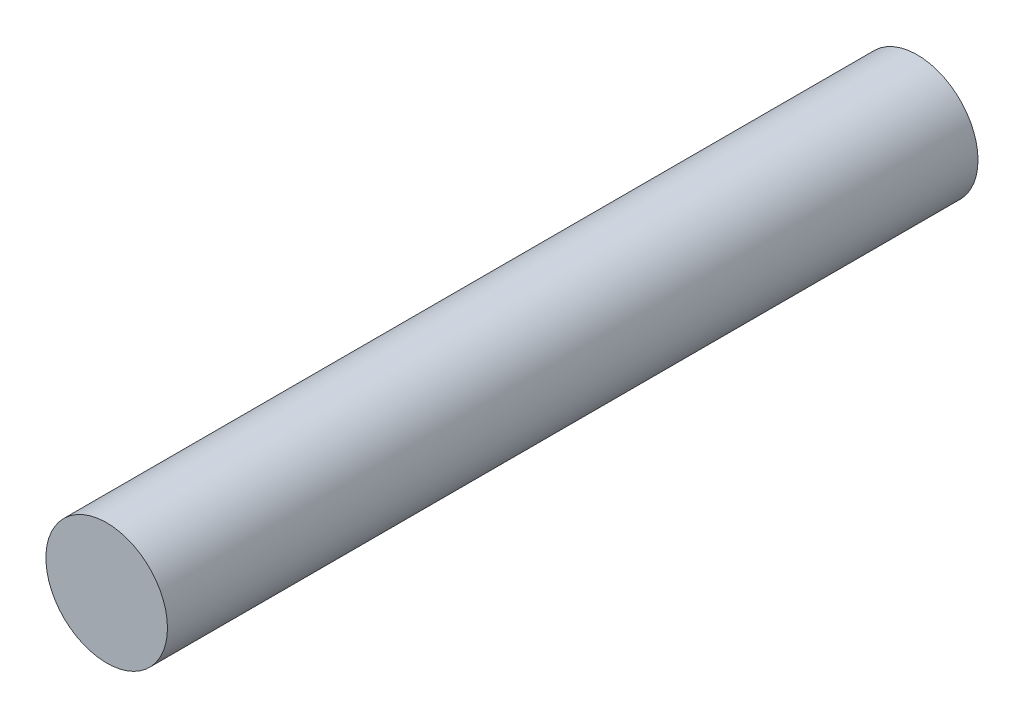
SolidWorks part; units mm, degrees
material "1.0044 (S275JR)"
ref_plane "Plan de face" through (0, 0, 0) normal (0, 0, 1) x (1, 0, 0)
ref_plane "Plan de dessus" through (0, 0, 0) normal (0, 1, 0) x (1, 0, 0)
ref_plane "Plan de droite" through (0, 0, 0) normal (1, 0, 0) x (0, 0, -1)
sketch "Esquisse1" plane through (0, 0, 0) normal (0, 0, 1) x (1, 0, 0)
  circle A0 centre (0, 0) radius 15
  dimension "D1" = 30
extrude "Boss.-Extru.1" add sketch "Esquisse1" along normal blind 200
sketch "Esquisse2" plane through (0, 0, 0) normal (0, 0, -1) x (-1, 0, 0)
  line L1 (-13, 5) -> (12, 5)
  line L2 (-13, 5) -> (-13, -5)
  line L3 (-13, -5) -> (12, -5)
  line L4 (12, 5) -> (12, -5)
  dimension "D1" = 10
  dimension "D2" = 5
  dimension "D3" = 25
  dimension "D4" = 12
extrude "Enlèv. mat.-Extru.3" cut sketch "Esquisse2" against normal blind 2
